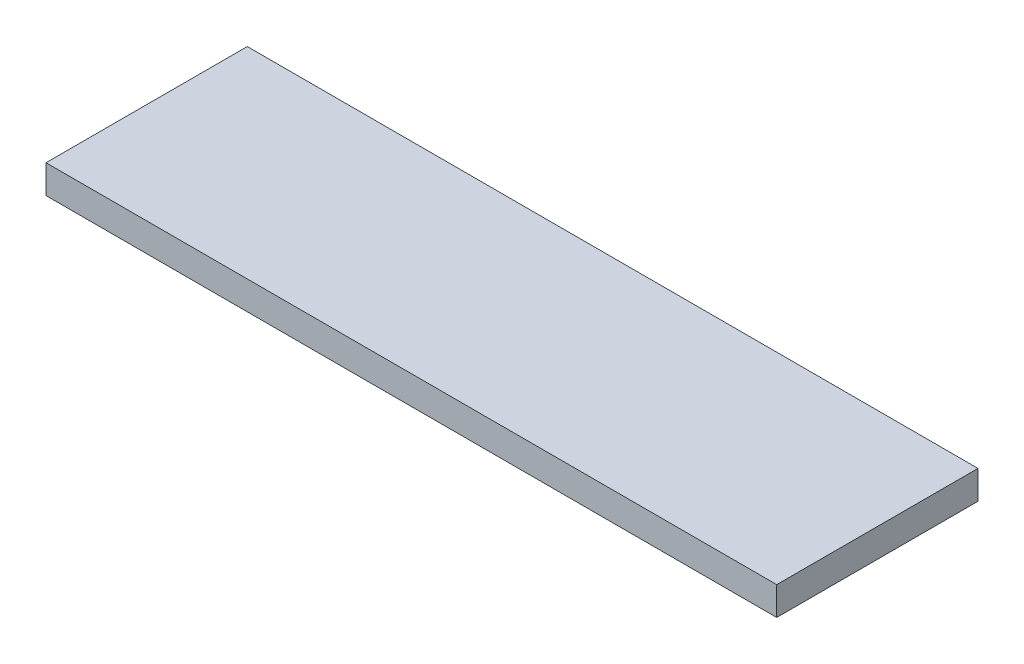
SolidWorks part; units mm, degrees
ref_plane "Front Plane" through (0, 0, 0) normal (0, 0, 1) x (1, 0, 0)
ref_plane "Top Plane" through (0, 0, 0) normal (0, 1, 0) x (1, 0, 0)
ref_plane "Right Plane" through (0, 0, 0) normal (1, 0, 0) x (0, 0, -1)
sketch "Sketch1" plane through (0, 0, 0) normal (0, 1, 0) x (1, 0, 0)
  line L0 (-38.4726, 6.7478) -> (-38.4726, 14.7478)
  line L1 (-30.4726, 14.7478) -> (38.5274, 14.7478)
  line L2 (-38.4726, 6.7478) -> (-38.4726, -6.4622)
  line L3 (-38.4726, -6.4622) -> (38.5274, -6.4622)
  line L4 (38.5274, 14.7478) -> (38.5274, -6.4622)
  line L5 (-38.4726, 14.7478) -> (-30.4726, 14.7478)
  point P0 (-38.4726, 14.7478)
  dimension "D1" = 77
  dimension "D2" = 21.21
extrude "Boss-Extrude1" add sketch "Sketch1" along normal blind 3
